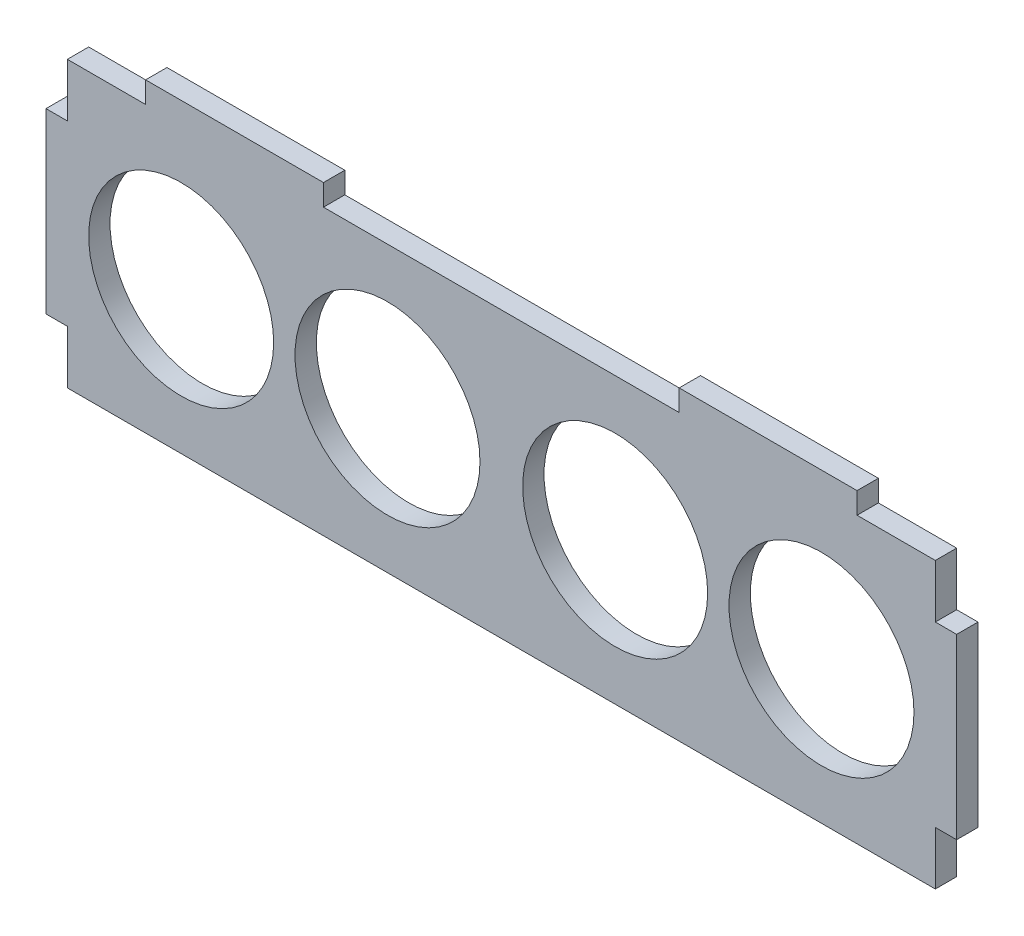
SolidWorks part; units mm, degrees
ref_plane "Front Plane" through (0, 0, 0) normal (0, 0, 1) x (1, 0, 0)
ref_plane "Top Plane" through (0, 0, 0) normal (0, 1, 0) x (1, 0, 0)
ref_plane "Right Plane" through (0, 0, 0) normal (1, 0, 0) x (0, 0, -1)
sketch "Sketch1" plane through (0, 0, 0) normal (0, 0, 1) x (1, 0, 0)
  line L0 (-64, 0) -> (64, 0) construction
  line L1 (-61, -20) -> (61, -20)
  line L2 (-61, -20) -> (-61, 20)
  line L3 (-61, 20) -> (61, 20)
  line L4 (61, -20) -> (61, 20)
  line L5 (-61, -20) -> (61, 20) construction
  line L6 (-61, 20) -> (61, -20) construction
  line L7 (-61, 12.5) -> (-64, 12.5)
  line L8 (-61, 12.5) -> (-61, -12.5)
  line L9 (-61, -12.5) -> (-64, -12.5)
  line L10 (-64, 12.5) -> (-64, -12.5)
  line L11 (61, 12.5) -> (64, 12.5)
  line L12 (61, 12.5) -> (61, -12.5)
  line L13 (61, -12.5) -> (64, -12.5)
  line L14 (64, 12.5) -> (64, -12.5)
  line L15 (-50, 20) -> (-25, 20)
  line L16 (-50, 20) -> (-50, 23)
  line L17 (-50, 23) -> (-25, 23)
  line L18 (-25, 20) -> (-25, 23)
  line L19 (25, 20) -> (50, 20)
  line L20 (25, 20) -> (25, 23)
  line L21 (25, 23) -> (50, 23)
  line L22 (50, 20) -> (50, 23)
  circle A0 centre (-45, 0) radius 13
  circle A1 centre (45, 0) radius 13
  circle A2 centre (-16, 0) radius 13
  circle A3 centre (16, 0) radius 13
  point P0 (0, 0)
  point P21 (-64, 0)
  point P22 (64, 0)
  point P33 (0, 0)
  dimension "D5" = 26
  dimension "D1" = 25
  dimension "D2" = 3
  dimension "D3" = 25
  dimension "D4" = 25
  dimension "D6" = 16
  dimension "D7" = 16
  dimension "D8" = 122
  dimension "D9" = 40
  dimension "D10" = 45
  dimension "D11" = 45
extrude "Boss-Extrude1" add sketch "Sketch1" along normal blind 3 contours L7 L10 L9 L2 | L3 L18 L17 L16 | L3 L22 L21 L20 | L14 L11 L4 L13 | L1 L4 L3 L2 A3 A2 A1 A0
